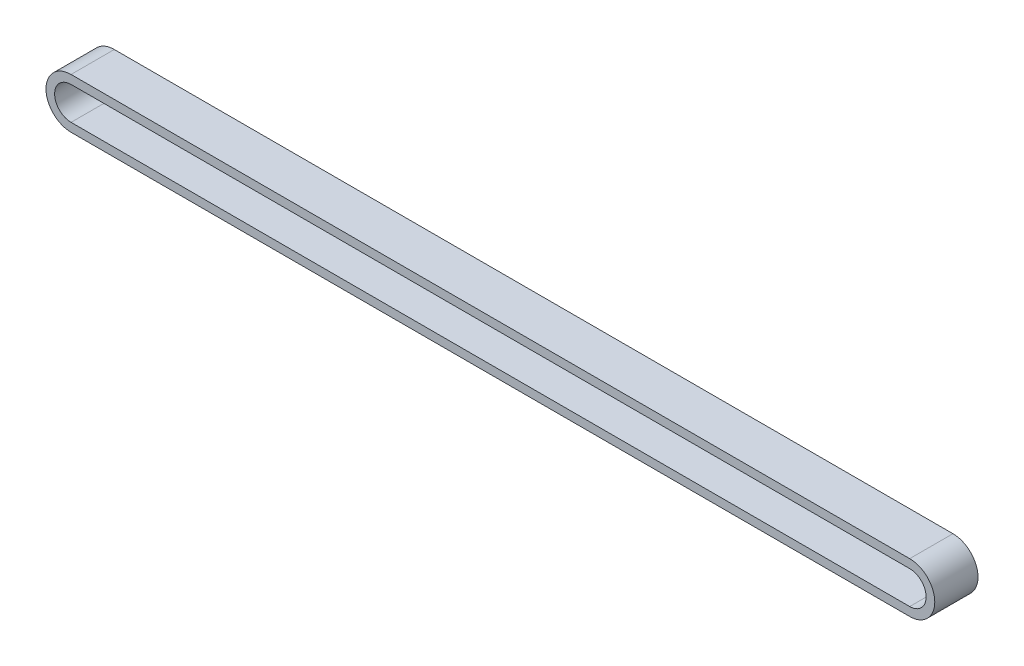
SolidWorks part; units mm, degrees
ref_plane "Front Plane" through (0, 0, 0) normal (0, 0, 1) x (1, 0, 0)
ref_plane "Top Plane" through (0, 0, 0) normal (0, 1, 0) x (1, 0, 0)
ref_plane "Right Plane" through (0, 0, 0) normal (1, 0, 0) x (0, 0, -1)
sketch "Sketch1" plane through (0, 0, 0) normal (0, 0, 1) x (1, 0, 0)
  line L0 (-204.0166, -6.2195) -> (-10.0166, -6.2195)
  line L1 (-10.0166, -13.8136) -> (-204.0166, -13.8136)
  line L2 (-204.0166, -4.2195) -> (-10.0166, -4.2195)
  line L3 (-10.0166, -15.8136) -> (-204.0166, -15.8136)
  arc A1 (-10.0166, -13.8136) -> (-10.0166, -6.2195) centre (-10.0166, -10.0166) ccw
  arc A3 (-204.0166, -6.2195) -> (-204.0166, -13.8136) centre (-204.0166, -10.0166) ccw
  arc A4 (-10.0166, -15.8136) -> (-10.0166, -4.2195) centre (-10.0166, -10.0166) ccw
  arc A5 (-204.0166, -4.2195) -> (-204.0166, -15.8136) centre (-204.0166, -10.0166) ccw
  dimension "D1" = 2
extrude "Boss-Extrude1" add sketch "Sketch1" along normal blind 10
